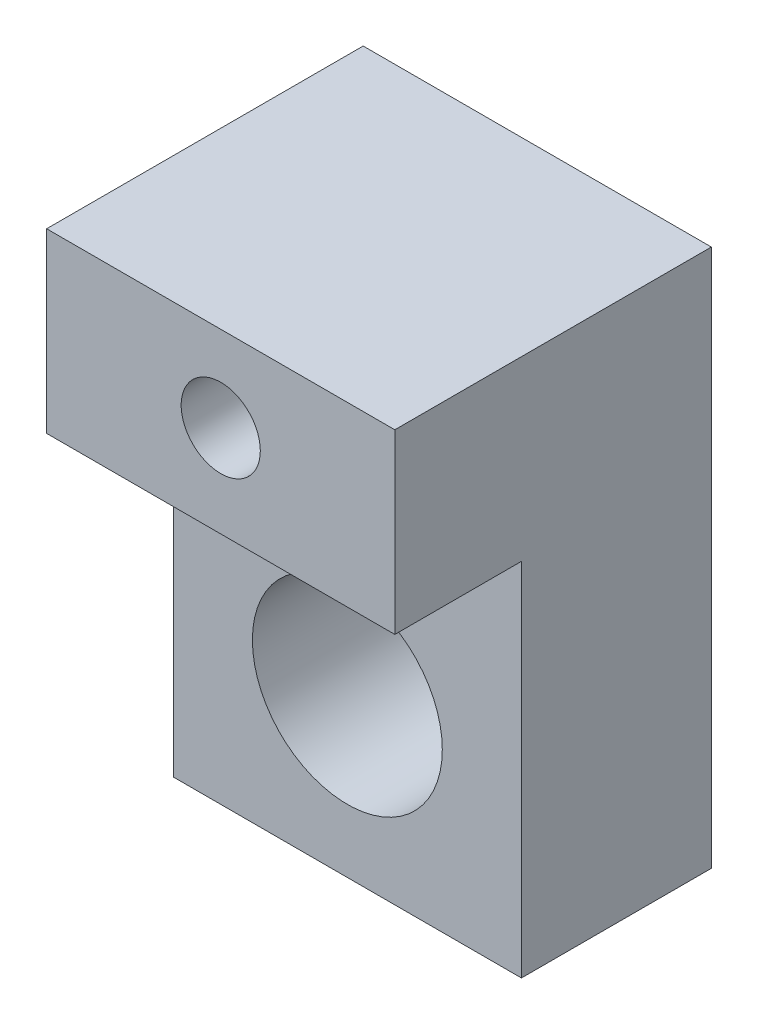
SolidWorks part; units mm, degrees
material "6061-T6 (SS)"
ref_plane "Front Plane" through (0, 0, 0) normal (0, 0, 1) x (1, 0, 0)
ref_plane "Top Plane" through (0, 0, 0) normal (0, 1, 0) x (1, 0, 0)
ref_plane "Right Plane" through (0, 0, 0) normal (1, 0, 0) x (0, 0, -1)
sketch "Sketch1" plane through (0, 0, 0) normal (0, 0, 1) x (1, 0, 0)
  line L1 (-2.75, 4.25) -> (2.75, 4.25)
  line L2 (-2.75, 4.25) -> (-2.75, -4.25)
  line L3 (-2.75, -4.25) -> (2.75, -4.25)
  line L4 (2.75, 4.25) -> (2.75, -4.25)
  dimension "D1" = 2.75
  dimension "D2" = 2.75
  dimension "D3" = 4.25
  dimension "D4" = 4.25
extrude "Boss-Extrude1" add sketch "Sketch1" along normal blind 3
sketch "Sketch4" plane through (0, 0, 3) normal (0, 0, 1) x (1, 0, 0)
  line L0 (-2.75, -4.25) -> (2.75, -4.25) construction
  circle A0 centre (0, -1.75) radius 1.5
  dimension "D1" = 2.5
  dimension "D2" = 3
extrude "Cut-Extrude1" cut sketch "Sketch4" against normal blind 10
sketch "Sketch7" plane through (0, 0, 0) normal (0, 0, -1) x (-1, 0, 0)
  line L0 (2.75, 4.25) -> (2.75, -4.25) construction
  line L1 (-2.75, 4.25) -> (2.75, 4.25)
  line L2 (-2.75, 4.25) -> (-2.75, 1.45)
  line L3 (-2.75, 1.45) -> (2.75, 1.45)
  line L4 (2.75, 4.25) -> (2.75, 1.45)
  dimension "D1" = 2.8
extrude "Boss-Extrude2" add sketch "Sketch7" against normal blind 5
sketch "Sketch8" plane through (0, 0, 5) normal (0, 0, 1) x (1, 0, 0)
  line L0 (-2.75, 4.25) -> (2.75, 4.25) construction
  point P0 (0, 2.9)
  point P1 (0, 4.25)
  dimension "D1" = 1.35
hole_wizard "M1.6x0.35 Tapped Hole1" positions "Sketch10" profile "Sketch9" tap size "M1.6x0.35" standard "Ansi Metric"
sketch "Sketch10" plane through (0, 0, 5) normal (0, 0, 1) x (1, 0, 0)
  point P0 (0, 2.9)
sketch "Sketch9" plane through (0, 2.9, 5) normal (1, 0, 0) x (0, -1, 0)
  line L0 (0, 0) -> (0, 4.3755)
  line L1 (0, 4.3755) -> (0.625, 4)
  line L2 (0.625, 4) -> (0.625, 0)
  line L5 (0.625, 0) -> (0, 0)
  line L10 (0, 4.3755) -> (-0.625, 4) construction
  line L11 (0, -6.35) -> (0, 107.95) construction
  dimension "ねじ下穴ﾄﾞﾘﾙ直径" = 1.25
  dimension "ねじ下穴ﾄﾞﾘﾙの深さ" = 4
  dimension "ﾄﾞﾘﾙ角度" = 118
cosmetic thread "Cosmetic Thread1" parameters "D1"=3.2, "D2"=1.6
